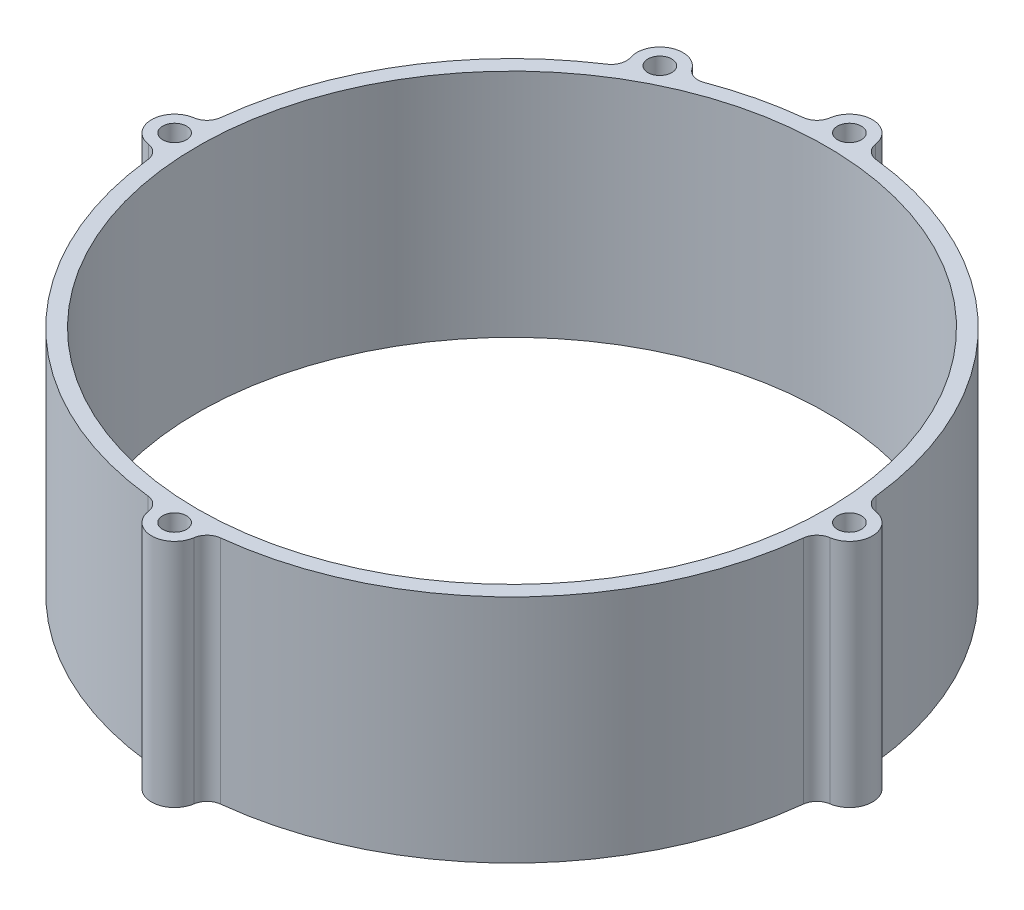
SolidWorks part; units mm, degrees
material "6061 合金"
ref_plane "前视基准面" through (0, 0, 0) normal (0, 0, 1) x (1, 0, 0)
ref_plane "上视基准面" through (0, 0, 0) normal (0, 1, 0) x (1, 0, 0)
ref_plane "右视基准面" through (0, 0, 0) normal (1, 0, 0) x (0, 0, -1)
sketch "草图1" plane through (0, 0, 0) normal (0, 1, 0) x (1, 0, 0)
  line L0 (-31.9, 0) -> (-31.9, 46.9) construction
  circle A0 centre (0, 0) radius 40.9
  circle A1 centre (0, 0) radius 43.9 construction
  circle A2 centre (0, 0) radius 31.9 construction
  circle A4 centre (0, 0) radius 40.9 construction
  circle A5 centre (0, 43.9) radius 1.55
  circle A6 centre (43.9, 0) radius 1.55
  circle A7 centre (0, -43.9) radius 1.55
  circle A8 centre (-43.9, 0) radius 1.55
  arc A9 (2.9681, 44.336) -> (-2.9681, 44.336) centre (0, 43.9) ccw
  arc A10 (44.336, -2.9681) -> (44.336, 2.9681) centre (43.9, 0) ccw
  arc A11 (-2.9681, -44.336) -> (2.9681, -44.336) centre (0, -43.9) ccw
  arc A12 (-44.336, 2.9681) -> (-44.336, -2.9681) centre (-43.9, 0) ccw
  arc A14 (-42.6388, -4.7266) -> (-4.7266, -42.6388) centre (0, 0) ccw
  arc A15 (4.7266, -42.6388) -> (42.6388, -4.7266) centre (0, 0) ccw
  arc A16 (42.6388, 4.7266) -> (4.7266, 42.6388) centre (0, 0) ccw
  arc A17 (-4.7266, 42.6388) -> (-15.1153, 40.149) centre (0, 0) ccw
  circle A18 centre (-19.9, 39.1306) radius 1.55
  arc A22 (-44.336, -2.9681) -> (-42.6388, -4.7266) centre (-44.6267, -4.9469) cw
  arc A24 (2.9681, -44.336) -> (4.7266, -42.6388) centre (4.9469, -44.6267) cw
  arc A25 (-2.9681, -44.336) -> (-4.7266, -42.6388) centre (-4.9469, -44.6267) ccw
  arc A26 (44.336, -2.9681) -> (42.6388, -4.7266) centre (44.6267, -4.9469) ccw
  arc A27 (44.336, 2.9681) -> (42.6388, 4.7266) centre (44.6267, 4.9469) cw
  arc A28 (2.9681, 44.336) -> (4.7266, 42.6388) centre (4.9469, 44.6267) ccw
  arc A29 (-4.7266, 42.6388) -> (-2.9681, 44.336) centre (-4.9469, 44.6267) ccw
  arc A30 (-17.452, 40.8646) -> (-22.7433, 38.1737) centre (-19.9, 39.1306) ccw
  arc A32 (-23.5414, 35.8638) -> (-42.6388, 4.7266) centre (0, 0) ccw
  arc A33 (-17.452, 40.8646) -> (-15.1153, 40.149) centre (-15.8199, 42.0207) ccw
  arc A34 (-22.7433, 38.1737) -> (-23.5414, 35.8638) centre (-24.6389, 37.5358) cw
  arc A35 (-44.336, 2.9681) -> (-42.6388, 4.7266) centre (-44.6267, 4.9469) ccw
  point P11 (0, 46.9)
  point P34 (-21.8963, 36.8912)
  point P52 (2.7945, -42.8089)
  point P59 (42.8089, 2.7945)
  dimension "D1" = 81.8
  dimension "D3" = 9
  dimension "D6" = 3.1
  dimension "D8" = 6
  dimension "D12" = 2
  dimension "D9" = 2
  dimension "D5" = 12
  dimension "D2" = 3
  dimension "D4" = 4
  dimension "D7" = 4
extrude "凸台-拉伸1" add sketch "草图1" along normal blind 30
